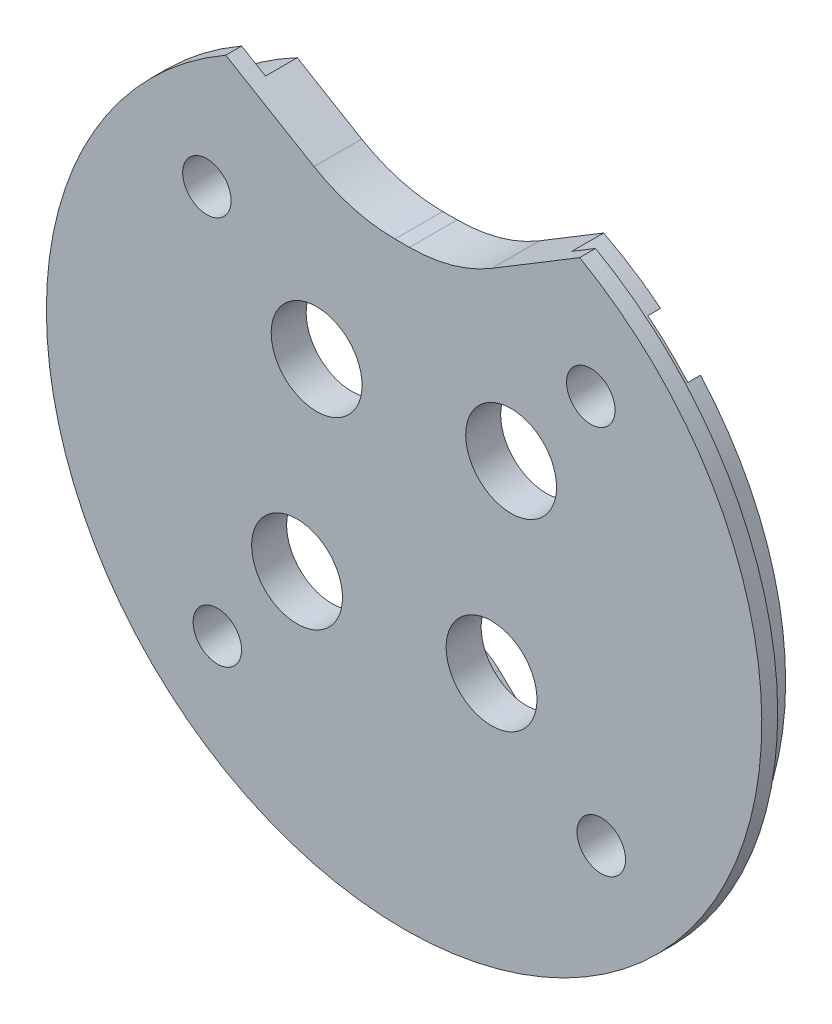
SolidWorks part; units mm, degrees
ref_plane "Front Plane" through (0, 0, 0) normal (0, 0, 1) x (1, 0, 0)
ref_plane "Top Plane" through (0, 0, 0) normal (0, 1, 0) x (1, 0, 0)
ref_plane "Right Plane" through (0, 0, 0) normal (1, 0, 0) x (0, 0, -1)
sketch "Sketch1" plane through (0, 0, 0) normal (0, 0, 1) x (1, 0, 0)
  circle A0 centre (0, 0) radius 21
  dimension "D1" = 42
extrude "Boss-Extrude1" add sketch "Sketch1" along normal blind 2
sketch "Sketch2" plane through (0, 0, 2) normal (0, 0, 1) x (1, 0, 0)
  circle A0 centre (0, 0) radius 22.5
  dimension "D1" = 45
extrude "Boss-Extrude2" add sketch "Sketch2" along normal blind 1
sketch "Sketch3" plane through (0, 0, 0) normal (0, 0, -1) x (-1, 0, 0)
  line L24 (15.5366, 14.5274) -> (15.3514, 14.7229)
  line L25 (8.544, 2.5289) -> (15.3863, 9.0083)
  line L26 (14.8732, -9.8324) -> (8.3937, -2.9901)
  line L27 (14.5274, -15.5366) -> (14.7229, -15.3514)
  line L28 (2.5289, -8.544) -> (9.0083, -15.3863)
  line L29 (-9.8324, -14.8732) -> (-2.9901, -8.3937)
  line L30 (-15.5366, -14.5274) -> (-15.3514, -14.7229)
  line L31 (-8.544, -2.5289) -> (-15.3863, -9.0083)
  line L32 (-14.8732, 9.8324) -> (-8.3937, 2.9901)
  line L33 (-14.5274, 15.5366) -> (-14.7229, 15.3514)
  line L34 (-2.5289, 8.544) -> (-9.0083, 15.3863)
  line L35 (9.8324, 14.8732) -> (2.9901, 8.3937)
  arc A24 (15.3514, 14.7229) -> (9.8324, 14.8732) centre (12.5168, 12.0385) ccw
  arc A25 (15.3863, 9.0083) -> (15.5366, 14.5274) centre (12.7019, 11.843) ccw
  arc A26 (8.544, 2.5289) -> (8.3937, -2.9901) centre (11.2283, -0.3058) ccw
  arc A27 (14.7229, -15.3514) -> (14.8732, -9.8324) centre (12.0385, -12.5168) ccw
  arc A28 (9.0083, -15.3863) -> (14.5274, -15.5366) centre (11.843, -12.7019) ccw
  arc A29 (2.5289, -8.544) -> (-2.9901, -8.3937) centre (-0.3058, -11.2283) ccw
  arc A30 (-15.3514, -14.7229) -> (-9.8324, -14.8732) centre (-12.5168, -12.0385) ccw
  arc A31 (-15.3863, -9.0083) -> (-15.5366, -14.5274) centre (-12.7019, -11.843) ccw
  arc A32 (-8.544, -2.5289) -> (-8.3937, 2.9901) centre (-11.2283, 0.3058) ccw
  arc A33 (-14.7229, 15.3514) -> (-14.8732, 9.8324) centre (-12.0385, 12.5168) ccw
  arc A34 (-9.0083, 15.3863) -> (-14.5274, 15.5366) centre (-11.843, 12.7019) ccw
  arc A35 (-2.5289, 8.544) -> (2.9901, 8.3937) centre (0.3058, 11.2283) ccw
extrude "Cut-Extrude1" cut sketch "Sketch3" against normal blind 0.8
sketch "Sketch4" plane through (0, 0, 0) normal (0, 0, -1) x (-1, 0, 0)
  line L0 (-11.0406, 19.605) -> (-5.5185, 16.2613)
  line L1 (-0.339, 14.8154) -> (0.5675, 14.8154)
  line L2 (5.6655, 16.2124) -> (11.2191, 19.5034)
  line L3 (0, 17.764) -> (0, -3.3693) construction
  line L4 (0, 1.65) -> (0, -1.65) construction
  arc A0 (-11.0406, 19.605) -> (11.2191, 19.5034) centre (0, 0) cw
  circle A1 centre (0, 0) radius 22.5 construction
  arc A2 (0.5675, 14.8154) -> (5.6655, 16.2124) centre (0.5675, 24.8154) ccw
  arc A3 (-5.5185, 16.2613) -> (-0.339, 14.8154) centre (-0.339, 24.8154) ccw
  circle A4 centre (12.4028, 11.7451) radius 1.524 construction
  circle A5 centre (12.4028, 11.7451) radius 1.524
  circle A6 centre (11.7451, -12.4028) radius 1.524 construction
  circle A7 centre (11.7451, -12.4028) radius 1.524
  circle A8 centre (-12.4028, -11.7451) radius 1.524 construction
  circle A9 centre (-12.4028, -11.7451) radius 1.524
  circle A10 centre (-11.7451, 12.4028) radius 1.524 construction
  circle A11 centre (-11.7451, 12.4028) radius 1.524
  circle A12 centre (6.7316, 6.3747) radius 2.8575 construction
  circle A13 centre (-5.5014, 5.8095) radius 2.8575
  circle A14 centre (-5.5014, 5.8095) radius 2.8575 construction
  circle A15 centre (6.7316, 6.3747) radius 2.8575 construction
  circle A16 centre (5.5014, -5.8095) radius 2.8575 construction
  circle A17 centre (5.5014, -5.8095) radius 2.8575 construction
  circle A18 centre (6.7316, -6.3747) radius 2.8575
  circle A19 centre (-6.7316, -6.3747) radius 2.8575
  circle A20 centre (-6.7316, -6.3747) radius 2.8575 construction
  circle A21 centre (5.5014, 5.8095) radius 2.8575
  circle A22 centre (-5.5014, -5.8095) radius 2.8575
  circle A23 centre (-6.7316, 6.3747) radius 2.8575
  spline S0 degree 3 poles (-1.2595, -31.5089) (1.4307, -31.4385) (2.3223, -31.3719) (4.0964, -31.1543) (4.9817, -31.0024) (7.6006, -30.4232) (9.2857, -29.877) (11.7243, -28.8244) (12.5223, -28.4346) (13.6966, -27.7899) (14.0851, -27.5644) (14.8475, -27.0972) (15.2218, -26.8553) (17.0594, -25.6048) (18.4217, -24.4743) (19.987, -22.895) (20.2931, -22.5708) (20.8913, -21.9054) (21.1832, -21.564) (22.0285, -20.5252) (22.5543, -19.8093) (23.5318, -18.3317) (23.9834, -17.57) (24.8107, -15.9995) (25.1869, -15.189) (26.1919, -12.6944) (26.6823, -10.9905) (27.1519, -8.3743) (27.2641, -7.4921) (27.3629, -6.1531) (27.3841, -5.7041) (27.4027, -4.8115) (27.4002, -4.3666) (27.3302, -2.1489) (27.0921, -0.3963) (26.4592, 2.1998) (26.2004, 3.0634) (25.6017, 4.7408) (25.261, 5.5585) (24.1191, 7.9511) (23.1988, 9.4678) (21.0391, 12.3316) (19.8362, 13.6319) (17.8577, 15.3962) (17.1691, 15.9532) (15.7333, 17.0045) (14.9822, 17.5009) (12.6845, 18.8669) (11.0855, 19.6224) (8.5884, 20.5279) (7.7396, 20.7917) (6.441, 21.1288) (6.004, 21.2314) (5.1308, 21.4147) (4.6934, 21.4959) (2.503, 21.8499) (0.739, 21.9685) (-1.4806, 21.9096) (-1.9253, 21.8874) (-2.8161, 21.8219) (-3.2632, 21.7785) (-4.5938, 21.6176) (-5.47, 21.4697) (-8.0665, 20.9065) (-9.7551, 20.3728) (-11.8109, 19.5003) (-12.2201, 19.315) (-13.0254, 18.9272) (-13.4221, 18.7243) (-14.5946, 18.0894) (-15.3529, 17.6309) (-16.8227, 16.6439) (-17.5342, 16.1153) (-18.5653, 15.2681) (-18.903, 14.9766) (-19.5659, 14.3749) (-19.8907, 14.065) (-21.4668, 12.4855) (-22.5886, 11.1143) (-23.8153, 9.2644) (-24.0518, 8.8875) (-24.5066, 8.1199) (-24.7256, 7.7281) (-25.3504, 6.5385) (-25.7226, 5.7303) (-26.71, 3.2618) (-27.1977, 1.5581) (-27.5831, -0.6479) (-27.6487, -1.0921) (-27.7559, -1.9778) (-27.7978, -2.4205) (-27.8885, -3.7481) (-27.9024, -4.6325) (-27.8384, -6.4) (-27.7607, -7.283) (-27.5124, -9.0479) (-27.3403, -9.9328) (-26.6957, -12.5238) (-26.0961, -14.1862) (-24.9482, -16.5848) (-24.5231, -17.3701) (-23.592, -18.9016) (-23.0923, -19.6378) (-21.4953, -21.7615) (-20.3016, -23.0654) (-18.3164, -24.8526) (-17.6188, -25.4221) (-16.1866, -26.4815) (-15.4495, -26.9742) (-13.1769, -28.3441) (-11.5806, -29.1144) (-9.0583, -30.0447) (-8.2076, -30.3127) (-6.4956, -30.7652) (-5.6329, -30.9501) (-3.0247, -31.3826) (-1.2595, -31.5089) (1.4307, -31.4385) (2.3223, -31.3719) knots -0.03125 -0.03125 0 0 0.015625 0.015625 0.03125 0.03125 0.0625 0.0625 0.078125 0.078125 0.085938 0.085938 0.09375 0.09375 0.125 0.125 0.132813 0.132813 0.140625 0.140625 0.15625 0.15625 0.171875 0.171875 0.1875 0.1875 0.21875 0.21875 0.234375 0.234375 0.242188 0.242188 0.25 0.25 0.28125 0.28125 0.296875 0.296875 0.3125 0.3125 0.34375 0.34375 0.375 0.375 0.390625 0.390625 0.40625 0.40625 0.4375 0.4375 0.453125 0.453125 0.460938 0.460938 0.46875 0.46875 0.5 0.5 0.507813 0.507813 0.515625 0.515625 0.53125 0.53125 0.5625 0.5625 0.570313 0.570313 0.578125 0.578125 0.59375 0.59375 0.609375 0.609375 0.617188 0.617188 0.625 0.625 0.65625 0.65625 0.664063 0.664063 0.671875 0.671875 0.6875 0.6875 0.71875 0.71875 0.726563 0.726563 0.734375 0.734375 0.75 0.75 0.765625 0.765625 0.78125 0.78125 0.8125 0.8125 0.828125 0.828125 0.84375 0.84375 0.875 0.875 0.890625 0.890625 0.90625 0.90625 0.9375 0.9375 0.953125 0.953125 0.96875 0.96875 1 1 1.015625 1.015625 1.03125 only from (0.534, -31.4619) to (0.534, -31.4619) construction
  dimension "D1" = 10
  dimension "D2" = 0
  dimension "D3" = 0
extrude "Cut-Extrude2" cut sketch "Sketch4" against normal up to next
